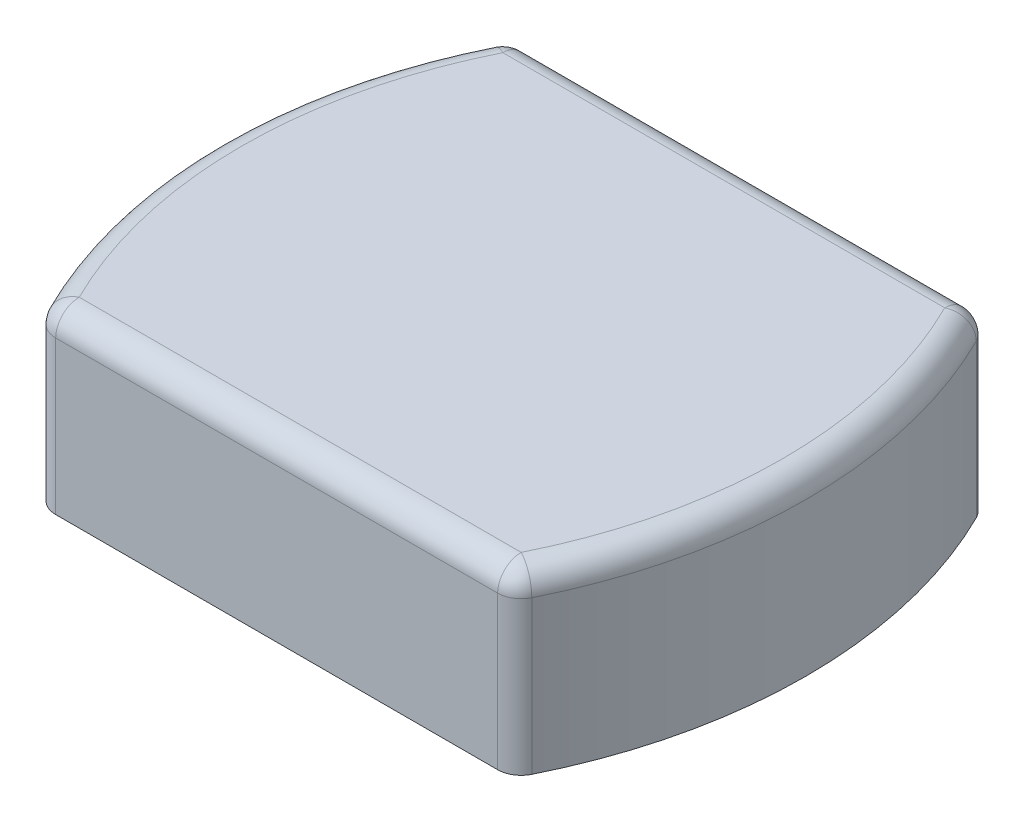
SolidWorks part; units mm, degrees
material "Very Low Density PE (SS)"
ref_plane "Front" through (0, 0, 0) normal (0, 0, 1) x (1, 0, 0)
ref_plane "Top" through (0, 0, 0) normal (0, 1, 0) x (1, 0, 0)
ref_plane "Right" through (0, 0, 0) normal (1, 0, 0) x (0, 0, -1)
sketch "Sketch1" plane through (0, 0, 0) normal (0, 1, 0) x (1, 0, 0)
  line L0 (-31.75, 0) -> (0, 0) construction
  line L1 (-25.4, 25.4) -> (25.4, 25.4)
  line L2 (-25.4, 25.4) -> (-25.4, -25.4)
  line L3 (-25.4, -25.4) -> (25.4, -25.4)
  line L4 (25.4, 25.4) -> (25.4, -25.4)
  line L5 (-25.4, 25.4) -> (25.4, -25.4) construction
  line L6 (-25.4, -25.4) -> (25.4, 25.4) construction
  arc A0 (-25.4, -25.4) -> (-25.4, 25.4) centre (22.225, 0) cw
  arc A1 (25.4, 25.4) -> (25.4, -25.4) centre (-22.225, 0) cw
  point P0 (0, 0)
  dimension "D1" = 50.8
  dimension "D2" = 31.75
extrude "Boss-Extrude1" add sketch "Sketch1" along normal blind 19.05 contours A0 L2 | A1 L4 | L4 L1 L2 L3
sketch "Sketch2" plane through (0, 0, 0) normal (0, -1, 0) x (1, 0, 0)
  line L1 (-22.86, 20.32) -> (22.86, 20.32)
  line L2 (-22.86, 20.32) -> (-22.86, -20.32)
  line L3 (-22.86, -20.32) -> (22.86, -20.32)
  line L4 (22.86, 20.32) -> (22.86, -20.32)
  line L5 (-22.86, 20.32) -> (22.86, -20.32) construction
  line L6 (-22.86, -20.32) -> (22.86, 20.32) construction
  point P0 (0, 0)
  dimension "D1" = 40.64
  dimension "D2" = 45.72
extrude "Cut-Extrude1" cut sketch "Sketch2" against normal offset from surface (15.875 mm away) 3.175 up to face at (0, 19.05, 0)
fillet "Fillet1" radius 2.54 8 edges at (25.4, 9.525, 25.4) (-25.4, 9.525, 25.4) (0, 19.05, 25.4) (31.75, 19.05, 0) (-31.75, 19.05, 0) (0, 19.05, -25.4) (-25.4, 9.525, -25.4) (25.4, 9.525, -25.4)
